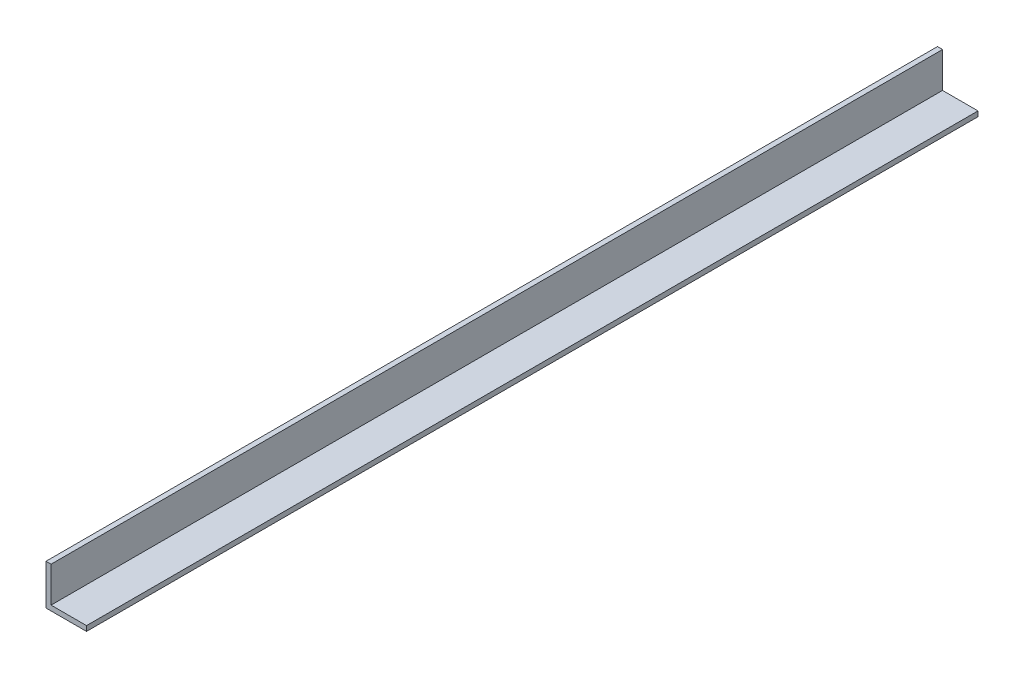
SolidWorks part; units mm, degrees
ref_plane "Front Plane" through (0, 0, 0) normal (0, 0, 1) x (1, 0, 0)
ref_plane "Top Plane" through (0, 0, 0) normal (0, 1, 0) x (1, 0, 0)
ref_plane "Right Plane" through (0, 0, 0) normal (1, 0, 0) x (0, 0, -1)
sketch "Sketch1" plane through (0, 0, 0) normal (0, 0, 1) x (1, 0, 0)
  line L0 (0, 25.4) -> (0, 0)
  line L1 (0, 0) -> (25.4, 0)
  line L2 (25.4, 0) -> (25.4, 3.175)
  line L3 (25.4, 3.175) -> (3.175, 3.175)
  line L4 (3.175, 3.175) -> (3.175, 25.4)
  line L5 (3.175, 25.4) -> (0, 25.4)
  dimension "D1" = 3.175
  dimension "D2" = 25.4
extrude "Boss-Extrude1" add sketch "Sketch1" along normal mid plane 558.8
